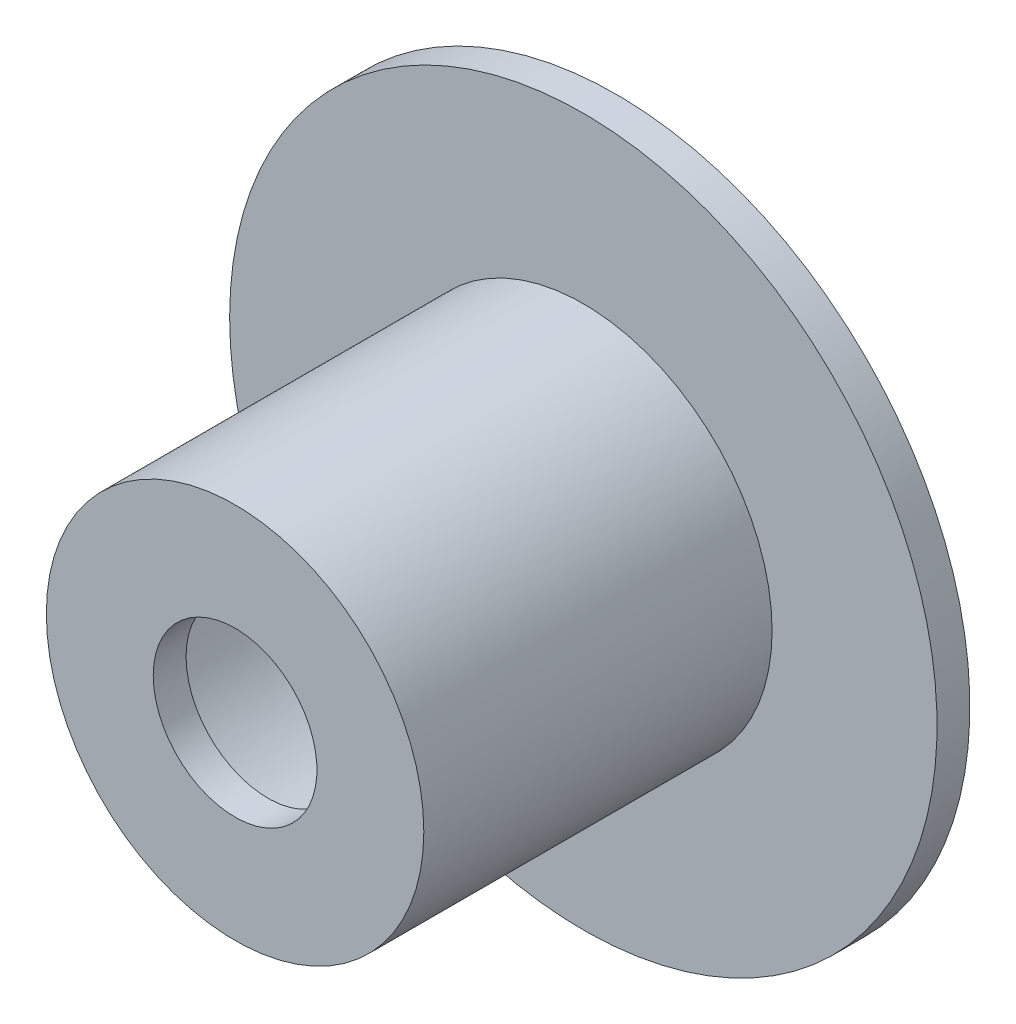
SolidWorks part; units mm, degrees
material "Alumina"
ref_plane "Front Plane" through (0, 0, 0) normal (0, 0, 1) x (1, 0, 0)
ref_plane "Top Plane" through (0, 0, 0) normal (0, 1, 0) x (1, 0, 0)
ref_plane "Right Plane" through (0, 0, 0) normal (1, 0, 0) x (0, 0, -1)
ref_plane "Plane1" through (259.3015, 0, 0) normal (-1, 0, 0) x (0, 0, 1)
sketch "Sketch2" plane through (259.3015, 0, 0) normal (-1, 0, 0) x (0, 0, 1)
  line L1 (0, -177.5737) -> (0, -119.5737) construction
  line L2 (4, -105.4706) -> (4, -125.5737)
  line L3 (-5, -148.5737) -> (52.0118, -148.5737) construction
  line L4 (4, -125.5737) -> (46.4382, -125.5737)
  line L5 (46.4382, -125.5737) -> (46.4382, -138.5992)
  line L6 (46.4382, -138.5992) -> (42.4382, -138.5992)
  line L7 (42.4382, -138.5992) -> (42.4382, -128.5737)
  line L8 (42.4382, -128.5737) -> (0, -128.5737)
  line L9 (0, -128.5737) -> (0, -105.4706)
  line L10 (0, -105.4706) -> (4, -105.4706)
  line L12 (35.5, -138.5992) -> (44, -138.5992) construction
  dimension "D1" = 4
  dimension "D2" = 0
  dimension "D3" = 4
  dimension "D6" = 0
  dimension "D4" = 23
  dimension "D5" = 20
revolve "Revolve1" add sketch "Sketch2" angle 360 about L3
equation "\"D4@Sketch2\"=\"External_IR@Thruster_Assembly.Assembly\""
equation "\"D5@Sketch2\"=\"D4@Sketch2\"-3"
